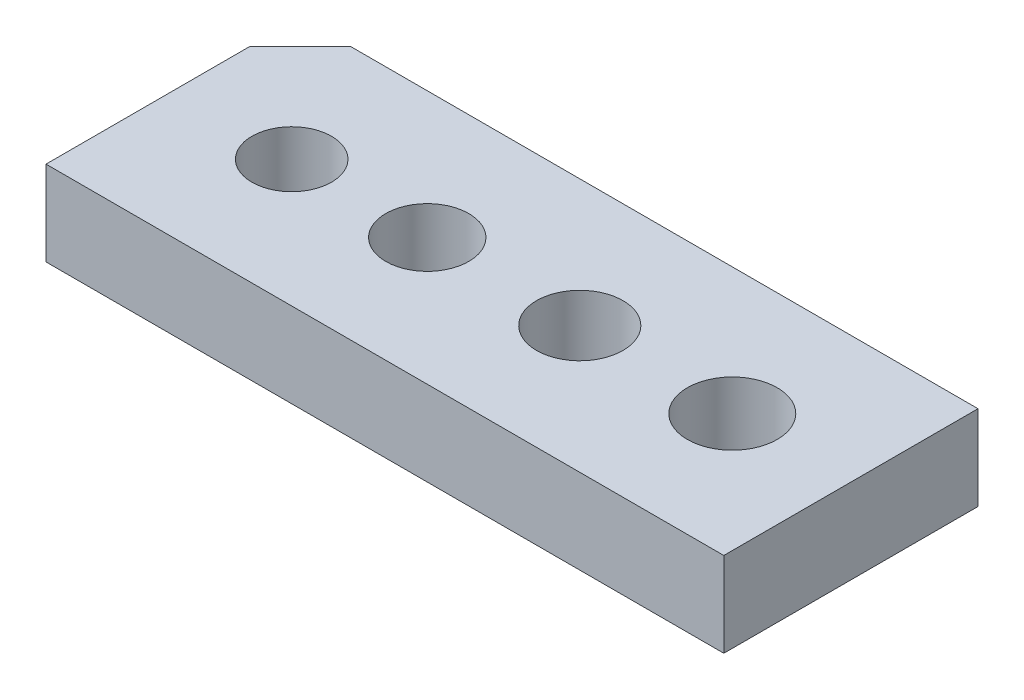
SolidWorks part; units mm, degrees
ref_plane "Front Plane" through (0, 0, 0) normal (0, 0, 1) x (1, 0, 0)
ref_plane "Top Plane" through (0, 0, 0) normal (0, 1, 0) x (1, 0, 0)
ref_plane "Right Plane" through (0, 0, 0) normal (1, 0, 0) x (0, 0, -1)
sketch "Sketch1" plane through (0, 0, 0) normal (0, 1, 0) x (1, 0, 0)
  line L0 (0, 0) -> (-20, 0) construction
  line L1 (-17, 7.5) -> (20, 7.5)
  line L2 (-20, 4.5) -> (-20, -7.5)
  line L3 (-20, -7.5) -> (20, -7.5)
  line L4 (20, 7.5) -> (20, -7.5)
  line L5 (-17.8182, 6.6818) -> (20, -7.5) construction
  line L6 (-20, -7.5) -> (20, 7.5) construction
  line L7 (0, 0) -> (20, 0) construction
  line L8 (-20, 4.5) -> (-17, 7.5)
  circle A0 centre (-13, 0) radius 2.35
  circle A2 centre (4, 0) radius 2.55
  circle A3 centre (13, 0) radius 2.65
  circle A4 centre (-5, 0) radius 2.45
  point P0 (0, 0)
  dimension "D3" = 4.7
  dimension "D4" = 4.9
  dimension "D5" = 5.1
  dimension "D6" = 5.3
  dimension "D1" = 15
  dimension "D2" = 40
  dimension "D7" = 7
  dimension "D8" = 8
  dimension "D9" = 7
  dimension "D10" = 9
  dimension "D11" = 135
extrude "Boss-Extrude1" add sketch "Sketch1" along normal blind 5
